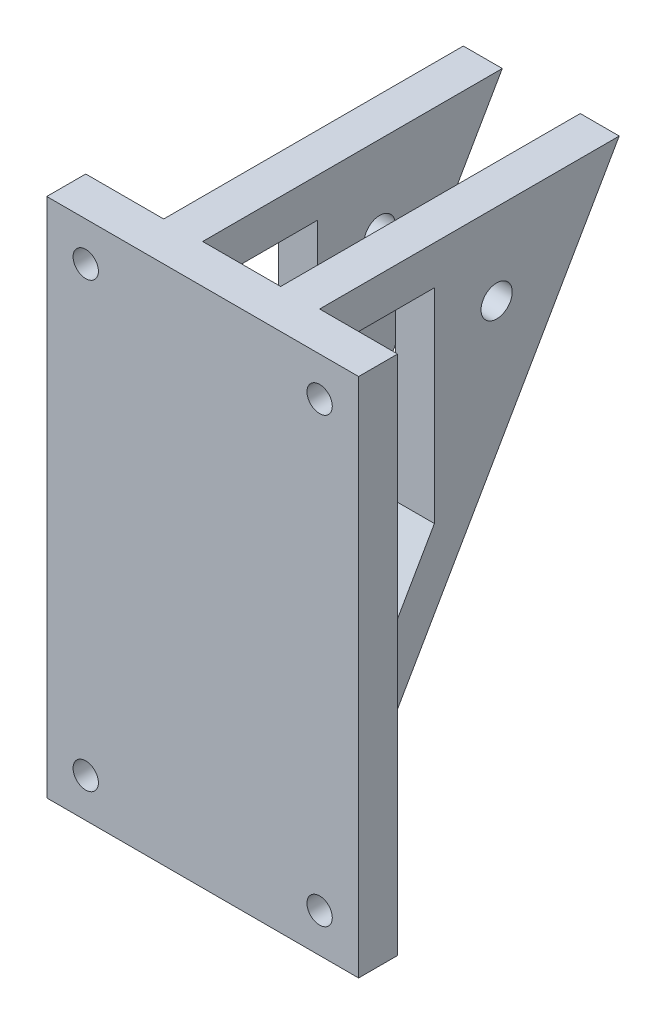
SolidWorks part; units mm, degrees
ref_plane "Plano frontal" through (0, 0, 0) normal (0, 0, 1) x (1, 0, 0)
ref_plane "Plano superior" through (0, 0, 0) normal (0, 1, 0) x (1, 0, 0)
ref_plane "Plano direito" through (0, 0, 0) normal (1, 0, 0) x (0, 0, -1)
ref_plane "Plano1" through (10, 0, 0) normal (1, 0, 0) x (0, 0, -1)
sketch "Esboço1" plane through (10, 0, 0) normal (1, 0, 0) x (0, 0, -1)
  line L0 (0, 0) -> (76.8605, 0)
  line L1 (76.8605, 0) -> (0, -133.6308)
  line L2 (0, -133.6308) -> (0, 0)
  line L3 (10, -10) -> (10, -96.1878)
  line L4 (10, -96.1878) -> (29.4416, -62.3864)
  line L5 (29.4416, -10) -> (10, -10)
  line L6 (29.4416, -62.3864) -> (29.4416, -10)
  circle A0 centre (45.4094, -20.9098) radius 4
  circle A1 centre (45.4094, -20.9098) radius 11 construction
  point P10 (45.4094, -20.9098)
  dimension "D5" = 8
  dimension "D4" = 22
  dimension "D1" = 10
  dimension "D2" = 10
  dimension "D3" = 10
extrude "Ressalto-extrusão2" add sketch "Esboço1" along normal blind 10
mirror "Espelhar2" about plane through (0, 0, 0) normal (1, 0, 0) of bodies 102
sketch "Esboço2" plane through (0, 0, 0) normal (0, 0, 1) x (1, 0, 0)
  line L0 (20, 0) -> (10, 0) construction
  line L1 (-40, 0) -> (40, 0)
  line L2 (-40, 0) -> (-40, -133.6308)
  line L3 (-40, -133.6308) -> (40, -133.6308)
  line L4 (40, 0) -> (40, -133.6308)
  line L5 (20, -133.6308) -> (10, -133.6308) construction
  line L6 (20, 0) -> (20, -133.6308) construction
  line L7 (-20, 0) -> (-20, -133.6308) construction
  circle A0 centre (-30, -10) radius 3.25
  circle A1 centre (30, -10) radius 3.25
  circle A2 centre (-30, -123.6308) radius 3.25
  circle A3 centre (30, -123.6308) radius 3.25
  point P20 (0, 0)
  point P21 (0, 0)
  point P22 (0, 0)
  point P23 (0, 0)
  point P24 (0, 0)
  point P25 (34.018, -6.8908)
  point P26 (30, -103.1353)
  dimension "D3" = 6.5
  dimension "D5" = 6.5
  dimension "D6" = 6.5
  dimension "D7" = 6.5
  dimension "D1" = 20
  dimension "D2" = 20
  dimension "D4" = 10
  dimension "D8" = 10
  dimension "D9" = 10
  dimension "D10" = 10
extrude "Ressalto-extrusão3" add sketch "Esboço2" along normal blind 10
equation "\"D2@Esboço2\"=\"D1@Esboço2\""
equation "\"D5@Esboço2\"=\"D3@Esboço2\""
equation "\"D6@Esboço2\"=\"D3@Esboço2\""
equation "\"D7@Esboço2\"=\"D3@Esboço2\""
